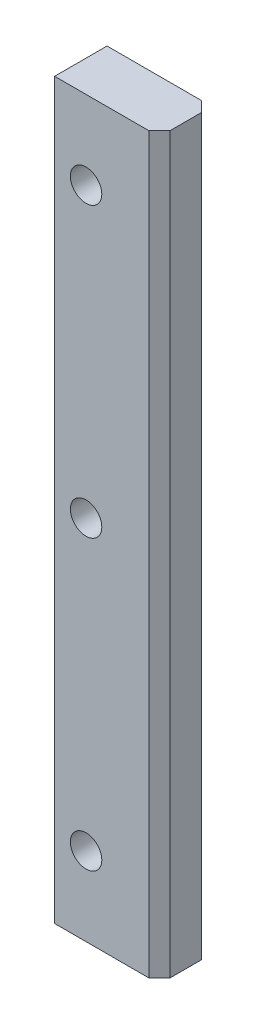
SolidWorks part; units mm, degrees
ref_plane "Front Plane" through (0, 0, 0) normal (0, 0, 1) x (1, 0, 0)
ref_plane "Top Plane" through (0, 0, 0) normal (0, 1, 0) x (1, 0, 0)
ref_plane "Right Plane" through (0, 0, 0) normal (1, 0, 0) x (0, 0, -1)
sketch "Sketch1" plane through (0, 0, 0) normal (0, 0, 1) x (1, 0, 0)
  line L0 (-10, -70) -> (-10, 70)
  line L1 (-10, 70) -> (10, 70)
  line L2 (10, 70) -> (10, -70)
  line L3 (10, -70) -> (-10, -70)
  line L4 (-82.3128, 0) -> (146.2829, 0) construction
  line L5 (0, 330.0605) -> (0, -326.1743) construction
  dimension "D1" = 20
  dimension "D2" = 140
extrude "Boss-Extrude1" add sketch "Sketch1" along normal blind 10
chamfer "Chamfer1" distance 2 angle 45 2 edges at (10, 0, 10) (10, 0, 0)
sketch "Sketch2" plane through (0, 0, 10) normal (0, 0, 1) x (1, 0, 0)
  line L0 (-39.0755, 0) -> (76.2606, 0) construction
  line L2 (-4, 181.9915) -> (-4, -71.9915) construction
  line L3 (-10, 70) -> (-10, -70) construction
  circle A0 centre (-4, 55) radius 3
  circle A1 centre (-4, 0) radius 3
  circle A2 centre (-4, -55) radius 3
  dimension "D3" = 6
  dimension "D1" = 110
  dimension "D2" = 6
extrude "Cut-Extrude1" cut sketch "Sketch2" against normal through all
